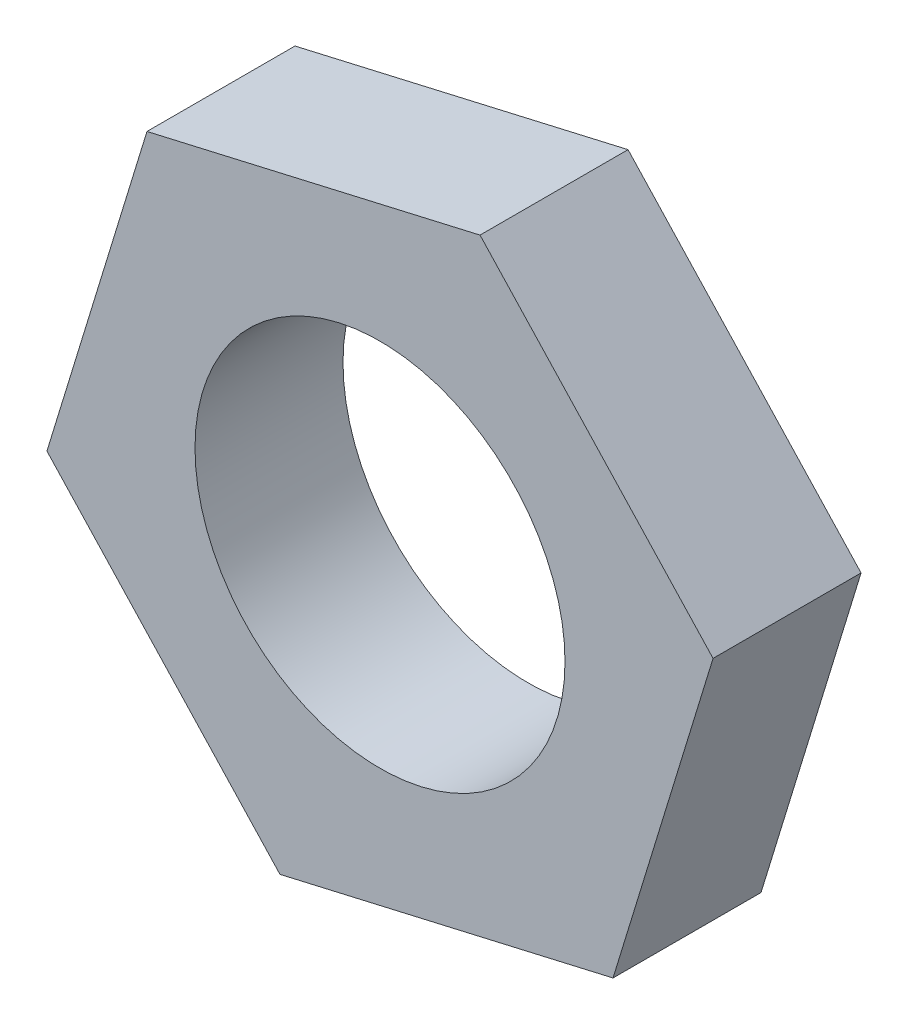
SolidWorks part; units mm, degrees
ref_plane "Face" through (0, 0, 0) normal (0, 0, 1) x (1, 0, 0)
ref_plane "Dessus" through (0, 0, 0) normal (0, 1, 0) x (1, 0, 0)
ref_plane "Droite" through (0, 0, 0) normal (1, 0, 0) x (0, 0, -1)
sketch "Esquisse1" plane through (0, 0, 0) normal (0, 0, 1) x (1, 0, 0)
  line L1 (-31.4889, 33.7903) -> (-45.0077, -10.375)
  line L2 (-45.0077, -10.375) -> (-13.5188, -44.1653)
  line L3 (-13.5188, -44.1653) -> (31.4889, -33.7903)
  line L4 (31.4889, -33.7903) -> (45.0077, 10.375)
  line L5 (45.0077, 10.375) -> (13.5188, 44.1653)
  line L6 (13.5188, 44.1653) -> (-31.4889, 33.7903)
  circle A0 centre (0, 0) radius 40 construction
  dimension "D1" = 80
extrude "Boss.-Extru.1" add sketch "Esquisse1" along normal blind 20
sketch "Esquisse2" plane through (0, 0, 20) normal (0, 0, 1) x (1, 0, 0)
  circle A0 centre (0, 0) radius 25
  dimension "D1" = 50
extrude "Enlèv. mat.-Extru.1" cut sketch "Esquisse2" against normal blind 20
